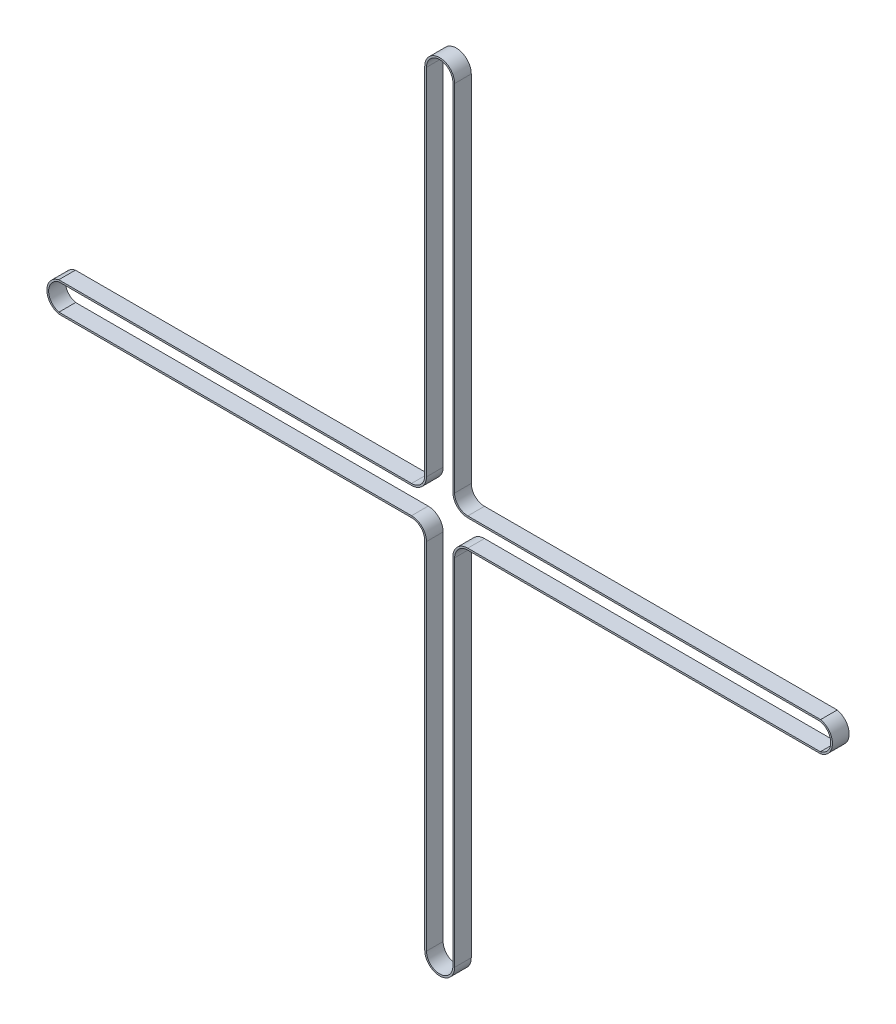
SolidWorks part; units mm, degrees
ref_plane "前视基准面" through (0, 0, 0) normal (0, 0, 1) x (1, 0, 0)
ref_plane "上视基准面" through (0, 0, 0) normal (0, 1, 0) x (1, 0, 0)
ref_plane "右视基准面" through (0, 0, 0) normal (1, 0, 0) x (0, 0, -1)
sketch "草图1" plane through (0, 0, 0) normal (0, 0, 1) x (1, 0, 0)
  line L0 (0, 13.9003) -> (0, -15.2482) construction
  line L1 (-185.0469, -130.1523) -> (161.1174, -130.1523) construction
  line L2 (-4.75, 7.6942) -> (-4.75, -120.0558)
  line L3 (-10.13, -125.4358) -> (-137.13, -125.4358)
  line L4 (-4.75, -267.9988) -> (-4.75, -140.2488)
  line L5 (-10.13, -134.8688) -> (-137.13, -134.8688)
  line L6 (10.13, -134.8688) -> (137.13, -134.8688)
  line L7 (4.75, -267.9988) -> (4.75, -140.2488)
  line L8 (10.13, -125.4358) -> (137.13, -125.4358)
  line L9 (4.75, 7.6942) -> (4.75, -120.0558)
  line L10 (-5.38, 7.6942) -> (-5.38, -120.0558)
  line L11 (-10.13, -124.8058) -> (-137.2021, -124.8058)
  line L12 (-10.13, -135.4988) -> (-137.2021, -135.4988)
  line L13 (-5.38, -267.9988) -> (-5.38, -140.2488)
  line L14 (5.38, -267.9988) -> (5.38, -140.2488)
  line L15 (10.13, -135.4988) -> (137.2021, -135.4988)
  line L16 (10.13, -124.8058) -> (137.2021, -124.8058)
  line L17 (5.38, 7.6942) -> (5.38, -120.0558)
  arc A0 (-4.75, 7.6942) -> (4.75, 7.6942) centre (0, 7.6942) cw
  arc A1 (-4.75, -267.9988) -> (4.75, -267.9988) centre (0, -267.9988) ccw
  arc A2 (-4.75, -120.0558) -> (-10.13, -125.4358) centre (-10.13, -120.0558) cw
  arc A3 (-137.13, -125.4358) -> (-137.13, -134.8688) centre (-136, -130.1523) ccw
  arc A4 (-4.75, -140.2488) -> (-10.13, -134.8688) centre (-10.13, -140.2488) ccw
  arc A5 (137.13, -125.4358) -> (137.13, -134.8688) centre (136, -130.1523) cw
  arc A6 (4.75, -140.2488) -> (10.13, -134.8688) centre (10.13, -140.2488) cw
  arc A7 (4.75, -120.0558) -> (10.13, -125.4358) centre (10.13, -120.0558) ccw
  arc A8 (-5.38, -120.0558) -> (-10.13, -124.8058) centre (-10.13, -120.0558) cw
  arc A9 (-137.2021, -124.8058) -> (-137.2021, -135.4988) centre (-136, -130.1523) ccw
  arc A10 (-5.38, -140.2488) -> (-10.13, -135.4988) centre (-10.13, -140.2488) ccw
  arc A11 (-5.38, -267.9988) -> (5.38, -267.9988) centre (0, -267.9988) ccw
  arc A12 (5.38, -140.2488) -> (10.13, -135.4988) centre (10.13, -140.2488) cw
  arc A13 (137.2021, -124.8058) -> (137.2021, -135.4988) centre (136, -130.1523) cw
  arc A14 (5.38, -120.0558) -> (10.13, -124.8058) centre (10.13, -120.0558) ccw
  arc A15 (-5.38, 7.6942) -> (5.38, 7.6942) centre (0, 7.6942) cw
  dimension "D1" = 4.75
  dimension "D3" = 5.38
  dimension "D5" = 4.85
  dimension "D2" = 127.75
  dimension "D4" = 127
  dimension "D7" = 272
  dimension "D6" = 0.63
extrude "凸台-拉伸1" add sketch "草图1" along normal blind 6
